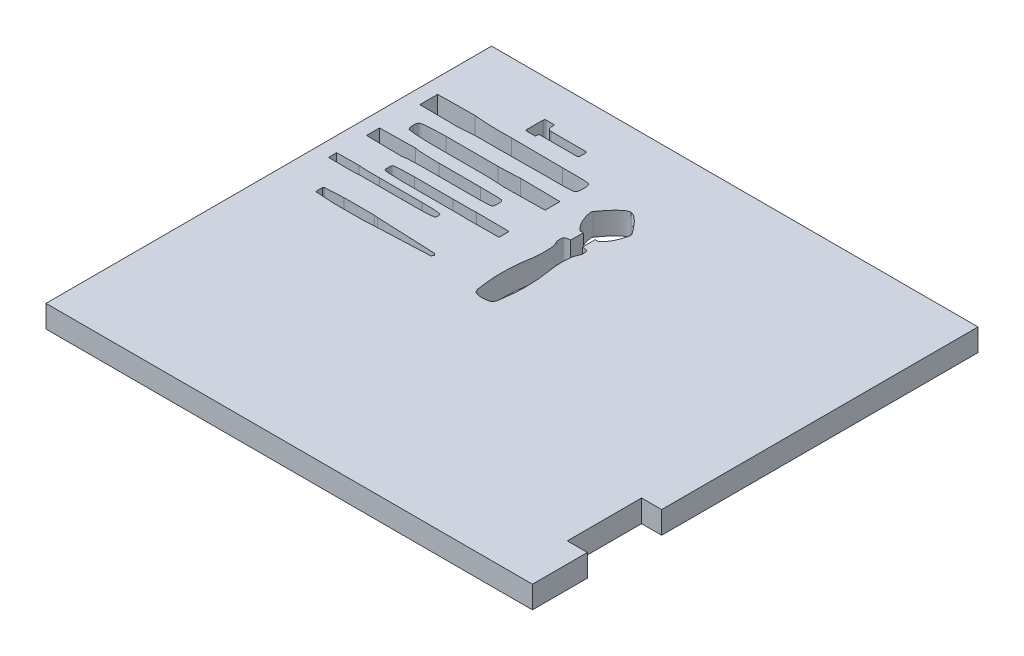
SolidWorks part; units mm, degrees
material "Tvrdý pěnový polyuretan"
ref_plane "Přední rovina" through (0, 0, 0) normal (0, 0, 1) x (1, 0, 0)
ref_plane "Horní rovina" through (0, 0, 0) normal (0, 1, 0) x (1, 0, 0)
ref_plane "Pravá rovina" through (0, 0, 0) normal (1, 0, 0) x (0, 0, -1)
sketch "Skica1" plane through (0, 0, 0) normal (0, 1, 0) x (1, 0, 0)
  line L1 (-327.5, 300) -> (327.5, 300)
  line L2 (-327.5, 300) -> (-327.5, -300)
  line L3 (-327.5, -300) -> (327.5, -300)
  line L4 (327.5, 300) -> (327.5, -300)
  line L5 (-327.5, 300) -> (327.5, -300) construction
  line L6 (-327.5, -300) -> (327.5, 300) construction
  point P0 (0, 0)
  dimension "D1" = 655
  dimension "D2" = 600
extrude "Přidat vysunutím1" add sketch "Skica1" along normal blind 30
sketch "Skica3" plane through (0, 30, 0) normal (0, 1, 0) x (1, 0, 0)
  line L0 (327.5, -300) -> (327.5, 300) construction
  line L1 (300.4586, -125.97) -> (354.5414, -125.97)
  line L2 (300.4586, -125.97) -> (300.4586, -225.97)
  line L3 (300.4586, -225.97) -> (354.5414, -225.97)
  line L4 (354.5414, -125.97) -> (354.5414, -225.97)
  line L5 (300.4586, -125.97) -> (354.5414, -225.97) construction
  line L6 (300.4586, -225.97) -> (354.5414, -125.97) construction
  point P0 (327.5, -175.97)
  dimension "D1" = 100
extrude "KONTROLA_100" cut sketch "Skica3" against normal through all
sketch "Skica4" plane through (0, 30, 0) normal (0, 1, 0) x (1, 0, 0)
  line L0 (-192.8488, 245.1527) -> (-193.2326, 250.4507)
  line L1 (-206.5475, 226.4507) -> (-206.5475, 248.4507)
  line L2 (-204.5475, 224.4507) -> (-193.2398, 224.4507)
  line L3 (-193.2398, 224.4507) -> (-192.6494, 228.0748)
  line L4 (-204.5475, 250.4507) -> (-193.2326, 250.4507)
  line L5 (-191.6624, 228.914) -> (-141.5475, 228.914)
  line L6 (-139.5475, 230.914) -> (-139.5475, 238.514)
  line L7 (-187.8618, 240.514) -> (-141.5475, 240.514)
  line L8 (-40.0348, -1.3572) -> (-40.0348, 204.3361) construction
  line L11 (-48.0348, 126.8183) -> (-48.0348, 144.0245)
  line L14 (-48.0348, 144.0245) -> (-52.5348, 144.0245)
  line L15 (-32.0348, 144.0245) -> (-27.5348, 144.0245)
  line L18 (-32.0348, 126.8183) -> (-32.0348, 144.0245)
  arc A0 (-206.5475, 226.4507) -> (-204.5475, 224.4507) centre (-204.5475, 226.4507) ccw
  arc A1 (-206.5475, 248.4507) -> (-204.5475, 250.4507) centre (-204.5475, 248.4507) cw
  arc A2 (-141.5475, 228.914) -> (-139.5475, 230.914) centre (-141.5475, 230.914) ccw
  arc A3 (-139.5475, 238.514) -> (-141.5475, 240.514) centre (-141.5475, 238.514) ccw
  arc A4 (-192.8488, 245.1527) -> (-187.8618, 240.514) centre (-187.8618, 245.514) ccw
  arc A5 (-192.6494, 228.0748) -> (-191.6624, 228.914) centre (-191.6624, 227.914) cw
  spline S0 degree 3 poles (-40.0348, 0.0245) (-44.0934, -0.0693) (-49.0531, 1.3306) (-50.8528, 2.4192) (-53.2465, 5.2206) (-54.2912, 13.1022) (-55.6516, 23.8082) (-56.5734, 36.6784) (-56.2748, 50.5696) (-55.7186, 62.8872) (-53.5439, 75.7502) (-51.8004, 87.3736) (-51.84, 100.2417) (-52.5901, 110.2664) (-56.1253, 116.7144) (-56.2238, 120.6685) (-56.338, 124.6399) (-54.5868, 125.6356) (-52.6042, 126.613) (-49.0346, 126.8652) (-48.316, 126.8285) (-48.0348, 126.8183) knots 0 0 0 0 0.061122 0.065239 0.079153 0.136804 0.218949 0.316069 0.392132 0.506228 0.569555 0.66126 0.74778 0.836872 0.864437 0.888075 0.923013 0.927486 0.939519 0.97254 0.978188 0.978188 0.978188 0.978188
  spline S1 degree 3 poles (-52.5348, 144.0245) (-56.7894, 147.6816) (-60.8102, 153.5789) (-63.7589, 160.5484) (-66.1714, 167.2499) (-66.4395, 171.2708) (-67.6629, 173.3867) (-63.3608, 179.519) (-60.3231, 183.5195) (-56.0692, 188.5623) (-52.403, 192.5544) (-48.9201, 195.571) (-45.7837, 198.0484) (-44.2181, 198.8658) (-42.7571, 199.4485) (-41.2626, 200.0245) (-40.0348, 200.0245) knots 0 0 0 0 0.287041 0.361746 0.417319 0.438297 0.471451 0.527971 0.663426 0.729021 0.795089 0.875047 0.930974 0.962796 0.981966 1 1 1 1
  spline S2 degree 3 poles (-27.5348, 144.0245) (-23.2802, 147.6816) (-19.2594, 153.5789) (-16.3107, 160.5484) (-13.8982, 167.2499) (-13.6301, 171.2708) (-12.4067, 173.3867) (-16.7088, 179.519) (-19.7465, 183.5195) (-24.0004, 188.5623) (-27.6667, 192.5544) (-31.1495, 195.571) (-34.2859, 198.0484) (-35.8515, 198.8658) (-37.3125, 199.4485) (-38.807, 200.0245) (-40.0348, 200.0245) knots 0 0 0 0 0.287041 0.361746 0.417319 0.438297 0.471451 0.527971 0.663426 0.729021 0.795089 0.875047 0.930974 0.962796 0.981966 1 1 1 1
  spline S3 degree 3 poles (-40.0348, 0.0245) (-35.9762, -0.0693) (-31.0165, 1.3306) (-29.2168, 2.4192) (-26.8232, 5.2206) (-25.7784, 13.1022) (-24.418, 23.8082) (-23.4962, 36.6784) (-23.7948, 50.5696) (-24.351, 62.8872) (-26.5257, 75.7502) (-28.2692, 87.3736) (-28.2296, 100.2417) (-27.4795, 110.2664) (-23.9443, 116.7144) (-23.8458, 120.6685) (-23.7316, 124.6399) (-25.4828, 125.6356) (-27.4654, 126.613) (-31.035, 126.8652) (-31.7536, 126.8285) (-32.0348, 126.8183) knots 0 0 0 0 0.061122 0.065239 0.079153 0.136804 0.218949 0.316069 0.392132 0.506228 0.569555 0.66126 0.74778 0.836872 0.864437 0.888075 0.923013 0.927486 0.939519 0.97254 0.978188 0.978188 0.978188 0.978188
  dimension "D4" = 2
  dimension "D5" = 5
  dimension "D6" = 1
  dimension "D1" = 67
  dimension "D2" = 11.6
  dimension "D3" = 26
  dimension "D7" = 16
  dimension "D8" = 200
  dimension "D9" = 54
  dimension "D10" = 56
  dimension "D11" = 32.3649
  dimension "D12" = 32.7227
  dimension "D13" = 24.1515
  dimension "D14" = 25
extrude "Odebrat vysunutím1" cut sketch "Skica4" against normal through all
sketch "Skica5" plane through (0, 30, 0) normal (0, 1, 0) x (1, 0, 0)
  line L0 (-306.4679, 195.4668) -> (-85.7762, 195.4668) construction
  line L1 (-307.5, 183.4668) -> (-307.5, 207.4668)
  line L2 (-307.5, 207.4668) -> (-257.5, 207.9668)
  line L3 (-206.8793, 206.3668) -> (-138.0174, 205.8668)
  line L4 (-206.8793, 184.5668) -> (-138.0174, 185.0668)
  line L5 (-307.5, 183.4668) -> (-257.5, 182.9668)
  line L6 (-183.2972, 145.1383) -> (-253.1808, 145.1383)
  line L7 (-99.1248, 154.6383) -> (-298.4094, 154.6383) construction
  line L8 (-100.138, 164.6383) -> (-100.138, 144.6383)
  line L9 (-183.2972, 164.1383) -> (-253.1808, 164.1383)
  line L10 (-100.138, 144.6383) -> (-153.8407, 143.8883)
  line L11 (-100.138, 164.6383) -> (-153.8407, 165.3883)
  line L12 (-308.4073, 120.3875) -> (-129.9539, 120.3875) construction
  line L13 (-307.5, 111.6375) -> (-307.5, 129.1375)
  line L14 (-307.5, 129.1375) -> (-259.5, 129.8875)
  line L15 (-226.1372, 128.1375) -> (-170.4533, 128.1375)
  line L16 (-226.1372, 112.6375) -> (-170.4533, 112.6375)
  line L17 (-307.5, 111.6375) -> (-259.5, 110.8875)
  line L18 (-99.4863, 95.5716) -> (-99.4863, 82.0716)
  line L19 (-174.9478, 82.0216) -> (-226.593, 82.0216)
  line L20 (-98.6448, 88.8216) -> (-264.1549, 88.8216) construction
  line L21 (-174.9478, 95.6216) -> (-226.593, 95.6216)
  line L22 (-99.4863, 82.0716) -> (-144.0048, 81.6716)
  line L23 (-99.4863, 95.5716) -> (-144.0048, 95.9716)
  line L24 (-307.5, 71.398) -> (-277.5, 71.648)
  line L25 (-307.5, 60.398) -> (-307.5, 71.398)
  line L26 (-308.266, 65.898) -> (-157.6104, 65.898) construction
  line L27 (-307.5, 60.398) -> (-277.5, 60.148)
  line L28 (-249.3341, 70.898) -> (-191.8011, 70.898)
  line L29 (-249.3341, 60.898) -> (-191.8011, 60.898)
  line L30 (-307.5, 280.7975) -> (-307.5, -260.8329) construction
  line L31 (-327.5, 300) -> (-327.5, -300) construction
  line L32 (-99.4863, 195.026) -> (-99.4863, -127.5107) construction
  line L33 (-283.4314, 17.1578) -> (-119.1241, 17.1578) construction
  line L34 (-121.5176, 17.1578) -> (-124.0176, 14.4078)
  line L35 (-124.0176, 14.4078) -> (-204.7729, 10.9078)
  line L36 (-204.7729, 10.9078) -> (-208.7421, 10.4078)
  line L37 (-208.7421, 10.4078) -> (-249.8722, 10.4078)
  line L38 (-249.8722, 10.4078) -> (-274.957, 11.8277)
  line L39 (-276.3722, 13.3253) -> (-276.3722, 20.9904)
  line L40 (-249.8722, 23.9078) -> (-274.957, 22.488)
  line L41 (-208.7421, 23.9078) -> (-249.8722, 23.9078)
  line L42 (-204.7729, 23.4078) -> (-208.7421, 23.9078)
  line L43 (-124.0176, 19.9078) -> (-204.7729, 23.4078)
  line L44 (-121.5176, 17.1578) -> (-124.0176, 19.9078)
  arc A0 (-274.957, 11.8277) -> (-276.3722, 13.3253) centre (-274.8722, 13.3253) cw
  arc A1 (-276.3722, 20.9904) -> (-274.957, 22.488) centre (-274.8722, 20.9904) cw
  spline S0 degree 3 poles (-138.0174, 205.8668) (-133.1693, 205.8316) (-122.8515, 205.8498) (-114.4037, 205.9442) (-105.5563, 205.5271) (-101.0697, 204.7722) (-100.1266, 202.6402) (-99.6909, 200.2484) (-99.5349, 197.956) (-99.4726, 196.5145) (-99.4908, 195.4668) knots 0 0 0 0 0.329375 0.579022 0.753141 0.82427 0.863457 0.895145 0.938345 1 1 1 1
  spline S1 degree 3 poles (-257.5, 207.9668) (-256.8252, 207.9735) (-246.9505, 206.7645) (-227.0644, 206.1938) (-216.21, 206.3545) (-213.9678, 206.4182) (-206.8793, 206.3668) knots 0 0 0 0 0.125665 0.22942 0.351473 1 1 1 1
  spline S2 degree 3 poles (-257.5, 182.9668) (-256.8252, 182.96) (-246.9505, 184.169) (-227.0644, 184.7397) (-216.21, 184.579) (-213.9678, 184.5153) (-206.8793, 184.5668) knots 0 0 0 0 0.125665 0.22942 0.351473 1 1 1 1
  spline S3 degree 3 poles (-138.0174, 185.0668) (-133.1692, 185.0668) (-122.8515, 185.0962) (-114.4037, 184.9873) (-105.5563, 185.4066) (-101.0697, 186.1613) (-100.1266, 188.2933) (-99.6909, 190.6852) (-99.5349, 192.9775) (-99.4726, 194.419) (-99.4908, 195.4668) knots 0 0 0 0 0.329375 0.579022 0.753141 0.82427 0.863457 0.895145 0.938345 1 1 1 1
  spline S4 degree 3 poles (-153.8407, 165.3883) (-156.381, 165.4238) (-158.1522, 164.9457) (-166.2488, 164.647) (-173.5089, 164.2476) (-178.1688, 164.1383) (-183.2972, 164.1383) knots 0 0 0 0 0.194961 0.326122 0.480415 1 1 1 1
  spline S5 degree 3 poles (-253.1808, 145.1383) (-257.5587, 145.1383) (-266.8755, 145.5109) (-274.6679, 145.7816) (-282.3496, 146.738) (-285.6906, 147.1347) (-286.7312, 148.3874) (-287.7243, 150.2963) (-287.9305, 152.3502) (-287.8606, 153.5049) (-287.9703, 154.6383) knots 0 0 0 0 0.329375 0.579022 0.753141 0.82427 0.863457 0.895145 0.938345 1 1 1 1
  spline S6 degree 3 poles (-153.8407, 143.8883) (-156.381, 143.8528) (-158.1522, 144.3309) (-166.2488, 144.6296) (-173.5089, 145.029) (-178.1688, 145.1383) (-183.2972, 145.1383) knots 0 0 0 0 0.194961 0.326122 0.480415 1 1 1 1
  spline S7 degree 3 poles (-253.1808, 164.1383) (-257.5587, 164.1383) (-266.8755, 163.7657) (-274.6679, 163.495) (-282.3496, 162.5386) (-285.6906, 162.1419) (-286.7312, 160.8892) (-287.7243, 158.9803) (-287.9305, 156.9264) (-287.8606, 155.7717) (-287.9703, 154.6383) knots 0 0 0 0 0.329375 0.579022 0.753141 0.82427 0.863457 0.895145 0.938345 1 1 1 1
  spline S8 degree 3 poles (-170.4533, 128.1375) (-166.533, 128.1375) (-158.101, 128.0332) (-152.3634, 127.9887) (-144.4437, 127.8222) (-141.0068, 127.3097) (-140.0119, 126.0434) (-139.4645, 124.9414) (-139.3424, 122.1952) (-139.2814, 123.5988) (-139.3018, 120.3875) knots 0 0 0 0 0.329375 0.579022 0.753141 0.82427 0.863457 0.895145 0.938345 1 1 1 1
  spline S9 degree 3 poles (-259.5, 129.8875) (-258.9544, 129.8976) (-256.3875, 128.9103) (-243.0394, 128.4455) (-235.4689, 128.1798) (-231.584, 128.1466) (-226.1372, 128.1375) knots 0 0 0 0 0.125665 0.22942 0.351473 1 1 1 1
  spline S10 degree 3 poles (-259.5, 110.8875) (-258.9544, 110.8774) (-256.3875, 111.8646) (-243.0394, 112.3295) (-235.4689, 112.5951) (-231.584, 112.6283) (-226.1372, 112.6375) knots 0 0 0 0 0.125665 0.22942 0.351473 1 1 1 1
  spline S11 degree 3 poles (-170.4533, 112.6375) (-166.533, 112.6375) (-158.101, 112.7418) (-152.3634, 112.7863) (-144.4437, 112.9528) (-141.0068, 113.4653) (-140.0119, 114.7316) (-139.4645, 115.8335) (-139.3424, 118.5797) (-139.2814, 117.1761) (-139.3018, 120.3875) knots 0 0 0 0 0.329375 0.579022 0.753141 0.82427 0.863457 0.895145 0.938345 1 1 1 1
  spline S12 degree 3 poles (-226.593, 82.0216) (-230.2289, 82.0216) (-239.9418, 82.2003) (-243.8164, 82.6466) (-251.0607, 82.6464) (-254.1662, 83.4601) (-255.143, 84.2496) (-255.4598, 85.7487) (-255.4475, 87.2913) (-255.504, 86.9729) (-255.485, 88.8216) knots 0 0 0 0 0.329375 0.579022 0.753141 0.82427 0.863457 0.895145 0.938345 1 1 1 1
  spline S13 degree 3 poles (-174.9478, 95.6216) (-167.9233, 95.6216) (-157.5296, 95.7467) (-146.1605, 95.6195) (-144.0048, 95.9716) knots 0 0 0 0 0.667268 1 1 1 1
  spline S14 degree 3 poles (-226.593, 95.6216) (-229.8217, 95.5027) (-240.0861, 95.4851) (-243.7928, 94.9898) (-251.0627, 94.9975) (-254.166, 94.1831) (-255.143, 93.3937) (-255.4598, 91.8945) (-255.4475, 90.352) (-255.504, 90.6704) (-255.485, 88.8216) knots 0 0 0 0 0.329375 0.579022 0.753141 0.82427 0.863457 0.895145 0.938345 1 1 1 1
  spline S15 degree 3 poles (-174.9478, 82.0216) (-167.9233, 82.0216) (-157.5296, 81.8966) (-146.1605, 82.0237) (-144.0048, 81.6716) knots 0 0 0 0 0.667268 1 1 1 1
  spline S16 degree 3 poles (-277.5, 71.648) (-275.2673, 71.2662) (-262.5373, 70.8167) (-252.8178, 70.898) (-249.3341, 70.898) knots 0 0 0 0 0.629859 1 1 1 1
  spline S17 degree 3 poles (-277.5, 60.148) (-275.2673, 60.5299) (-262.5373, 60.9794) (-252.8178, 60.898) (-249.3341, 60.898) knots 0 0 0 0 0.629859 1 1 1 1
  spline S18 degree 3 poles (-191.8011, 60.898) (-188.9589, 60.8758) (-176.5082, 61.0854) (-174.5414, 61.3375) (-170.8114, 61.6393) (-167.831, 62.078) (-165.9747, 62.6846) (-165.5976, 63.9072) (-165.4998, 64.4267) (-165.4922, 65.1328) (-165.5021, 65.898) knots 0 0 0 0 0.329375 0.579022 0.753141 0.82427 0.863457 0.895145 0.938345 1 1 1 1
  spline S19 degree 3 poles (-191.8011, 70.898) (-184.8873, 70.898) (-177.9506, 70.7185) (-174.3062, 70.4573) (-170.8315, 70.1568) (-167.8293, 69.718) (-165.975, 69.1114) (-165.5975, 67.8888) (-165.4998, 67.3693) (-165.4921, 66.6632) (-165.5021, 65.898) knots 0 0 0 0 0.329375 0.579022 0.753141 0.82427 0.863457 0.895145 0.938345 1 1 1 1
  point P33 (-307.5, 195.4668)
  point P67 (-100.138, 154.6383)
  point P101 (-307.5, 120.3875)
  point P135 (-99.4863, 88.8216)
  point P165 (-307.5, 65.898)
  point P172 (-100.138, 154.6383)
  point P183 (-276.3722, 17.1578)
  point P189 (-276.3722, 11.9078)
  point P192 (-276.3722, 22.4078)
  dimension "D11" = 50
  dimension "D33" = 1.5
  dimension "D2" = 50.6207
  dimension "D3" = 24
  dimension "D4" = 25
  dimension "D5" = 187.8323
  dimension "D6" = 168.1982
  dimension "D7" = 20
  dimension "D8" = 15.5
  dimension "D9" = 53.7028
  dimension "D10" = 19
  dimension "D12" = 17.5
  dimension "D13" = 19
  dimension "D14" = 48
  dimension "D15" = 155.9987
  dimension "D16" = 13.6
  dimension "D17" = 13.5
  dimension "D18" = 14.3
  dimension "D19" = 141.9979
  dimension "D20" = 11
  dimension "D21" = 30
  dimension "D22" = 10
  dimension "D23" = 28.1659
  dimension "D24" = 20
  dimension "D25" = 154.8546
  dimension "D26" = 13.5
  dimension "D27" = 83.2554
  dimension "D28" = 10.5
  dimension "D29" = 26.5
  dimension "D30" = 5.5
  dimension "D31" = 2.5
  dimension "D32" = 12.5
extrude "sekace" cut sketch "Skica5" against normal through all
